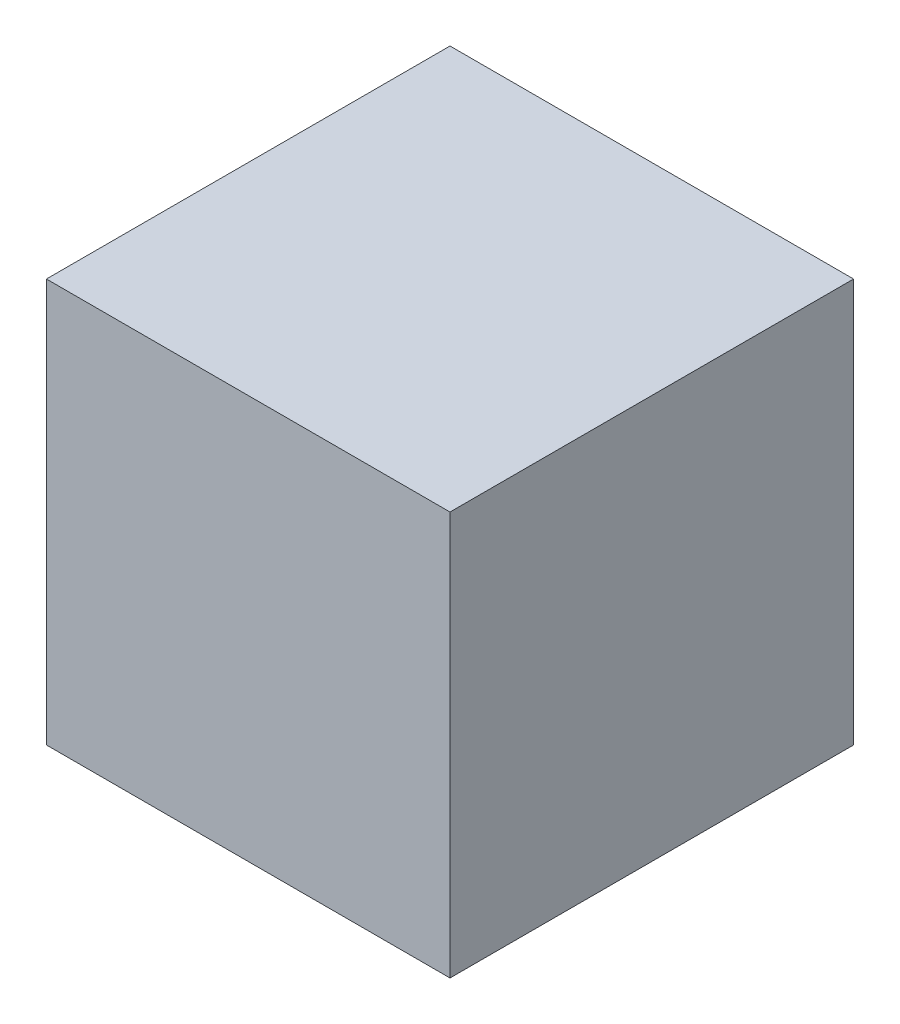
SolidWorks part; units mm, degrees
ref_plane "Front Plane" through (0, 0, 0) normal (0, 0, 1) x (1, 0, 0)
ref_plane "Top Plane" through (0, 0, 0) normal (0, 1, 0) x (1, 0, 0)
ref_plane "Right Plane" through (0, 0, 0) normal (1, 0, 0) x (0, 0, -1)
sketch "Sketch1" plane through (0, 0, 0) normal (1, 0, 0) x (0, 0, -1)
  line L1 (0, 0) -> (400, 0)
  line L2 (0, 0) -> (0, 400)
  line L3 (0, 400) -> (400, 400)
  line L4 (400, 0) -> (400, 400)
  dimension "D1" = 400
  dimension "D2" = 400
extrude "Boss-Extrude1" add sketch "Sketch1" along normal blind 400
